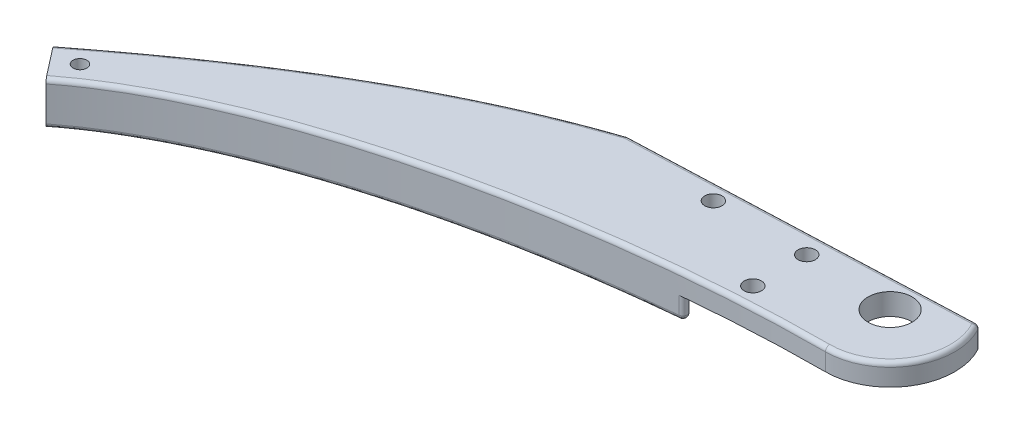
SolidWorks part; units mm, degrees
ref_plane "Front Plane" through (0, 0, 0) normal (0, 0, 1) x (1, 0, 0)
ref_plane "Top Plane" through (0, 0, 0) normal (0, 1, 0) x (1, 0, 0)
ref_plane "Right Plane" through (0, 0, 0) normal (1, 0, 0) x (0, 0, -1)
sketch "Sketch1" plane through (0, 0, 0) normal (0, 1, 0) x (1, 0, 0)
  line L0 (0, 0) -> (-143.2011, 0) construction
  line L1 (0, 0) -> (10.6066, 10.6066) construction
  line L2 (0, 0) -> (15, 0) construction
  line L3 (-143.2011, 0) -> (-143.2011, -44.6479) construction
  line L4 (-143.2011, -44.6479) -> (0, 0) construction
  line L5 (-150.2325, -43.7465) -> (-144.1674, -51.5547)
  circle A1 centre (0, 0) radius 15
  circle A3 centre (-143.2011, -44.6479) radius 5 construction
  circle A4 centre (-143.2011, -44.6479) radius 1.6
  spline S0 degree 3 poles (0, -15) (-49.2112, -15) (-112.5778, -27.017) (-144.1674, -51.5547) knots 0 0 0 0 1 1 1 1
  spline S1 degree 3 poles (0, 15) (-53.3333, 15) (-97.5832, -2.8503) (-150.2325, -43.7465) knots 0 0 0 0 1 1 1 1
  dimension "D1" = 150
  dimension "D2" = 30
  dimension "D4" = 9.887
  dimension "D7" = 200
  dimension "D8" = 160
  dimension "D3" = 10
  dimension "D6" = 3.2
  dimension "D9" = 147.6335
  dimension "D10" = 120
  dimension "D5" = 45
extrude "Boss-Extrude4" add sketch "Sketch1" along normal blind 10
sketch "Sketch2" plane through (0, 0, 0) normal (0, -1, 0) x (1, 0, 0)
  line L0 (15, 0) -> (0, 0) construction
  line L1 (0, 0) -> (16.383, -11.4715) construction
  line L2 (13.5946, 6.3393) -> (20.9146, -9.3584)
  circle A0 centre (0, 0) radius 15
  circle A1 centre (16.383, -11.4715) radius 5
  circle A2 centre (16.383, -11.4715) radius 1.5
  spline S0 degree 3 poles (-25.2326, -13.5779) (7.2847, -18.1763) (14.3784, -16.0523) (14.42, -16.0701) knots 0 0 0 0 1 1 1 1
  spline S1 degree 3 poles (0, -15) (-53.3333, -15) (-97.5832, 2.8503) (-150.2325, 43.7465) knots 0 0 0 0 1 1 1 1 construction
  spline M9 degree 3 poles (-150.2325, 43.7465) (-97.5832, 2.8503) (-53.3333, -15) (0, -15) knots 0 0 0 0 1 1 1 1
  arc M10 (0, -15) -> (0, 15) centre (0, 0) ccw
  dimension "D3" = 10
  dimension "D4" = 30
  dimension "D5" = 3
  dimension "D1" = 35
  dimension "D2" = 20
extrude "Boss-Extrude6" add sketch "Sketch2" against normal blind 5 contours S0 A1 L2 M9 M10 | A1 S0 A2
sketch "Sketch6" plane through (0, 10, 0) normal (0, 1, 0) x (1, 0, 0)
  line L0 (-65.409, 4.599) -> (12.8919, 7.668)
  line L1 (12.8919, 7.668) -> (7.2723, 26.2924)
  line L2 (7.2723, 26.2924) -> (-49.3026, 23.0614)
  line L3 (-49.3026, 23.0614) -> (-65.409, 4.599)
  arc A0 (0, -15) -> (0, 15) centre (0, 0) ccw construction
  spline S0 degree 3 poles (0, 15) (-53.3333, 15) (-97.5832, -2.8503) (-150.2325, -43.7465) knots 0 0 0 0 1 1 1 1 construction
extrude "Cut-Extrude2" cut sketch "Sketch6" against normal blind 5
sketch "Sketch9" plane through (0, 0, 0) normal (0, -1, 0) x (1, 0, 0)
  line L0 (-29.211, 16.2999) -> (-65.409, -4.599)
  line L1 (0, 37.0885) -> (0, -32.3472) construction
  line L2 (-29.211, 16.2999) -> (23.7993, 49.2746)
  line L3 (23.7993, 49.2746) -> (79.7877, -46.8224)
  line L4 (79.7877, -46.8224) -> (-53.1675, -38.2192)
  line L5 (-53.1675, -38.2192) -> (-65.409, -4.599)
  spline S0 degree 3 poles (0, 15) (-49.2112, 15) (-112.5778, 27.017) (-144.1674, 51.5547) knots 0 0 0 0 1 1 1 1 construction
  spline S1 degree 3 poles (-25.2326, -13.5779) (-67.8629, -8.6249) (-106.0963, 9.463) (-150.2325, 43.7465) knots 0.161695 0.161695 0.161695 0.161695 1 1 1 1 construction
  dimension "D1" = 60
  dimension "D2" = 28.7216
extrude "Cut-Extrude4" cut sketch "Sketch9" against normal blind 5
sketch "Sketch7" plane through (0, 10, 0) normal (0, 1, 0) x (1, 0, 0)
  circle A0 centre (0, 0) radius 5.1
  dimension "D1" = 10.2
extrude "Cut-Extrude3" cut sketch "Sketch7" against normal blind 10
fillet "Fillet8" radius 1 9 edges at (13.0388, 10, 7.4155) (-26.2585, 10, -6.1335) (-47.31, 0, 5.8505) (-29.211, 2.5, 16.2999) (12.8919, 7.5, -7.668)
sketch "Sketch11" plane through (0, 5, 0) normal (0, -1, 0) x (1, 0, 0)
  circle A0 centre (-20.676, 11.1567) radius 2
  circle A1 centre (-20.676, -1.3433) radius 2
  circle A2 centre (-42.3267, -1.3433) radius 2
  dimension "D1" = 4
extrude "Cut-Extrude5" cut sketch "Sketch11" against normal through all
